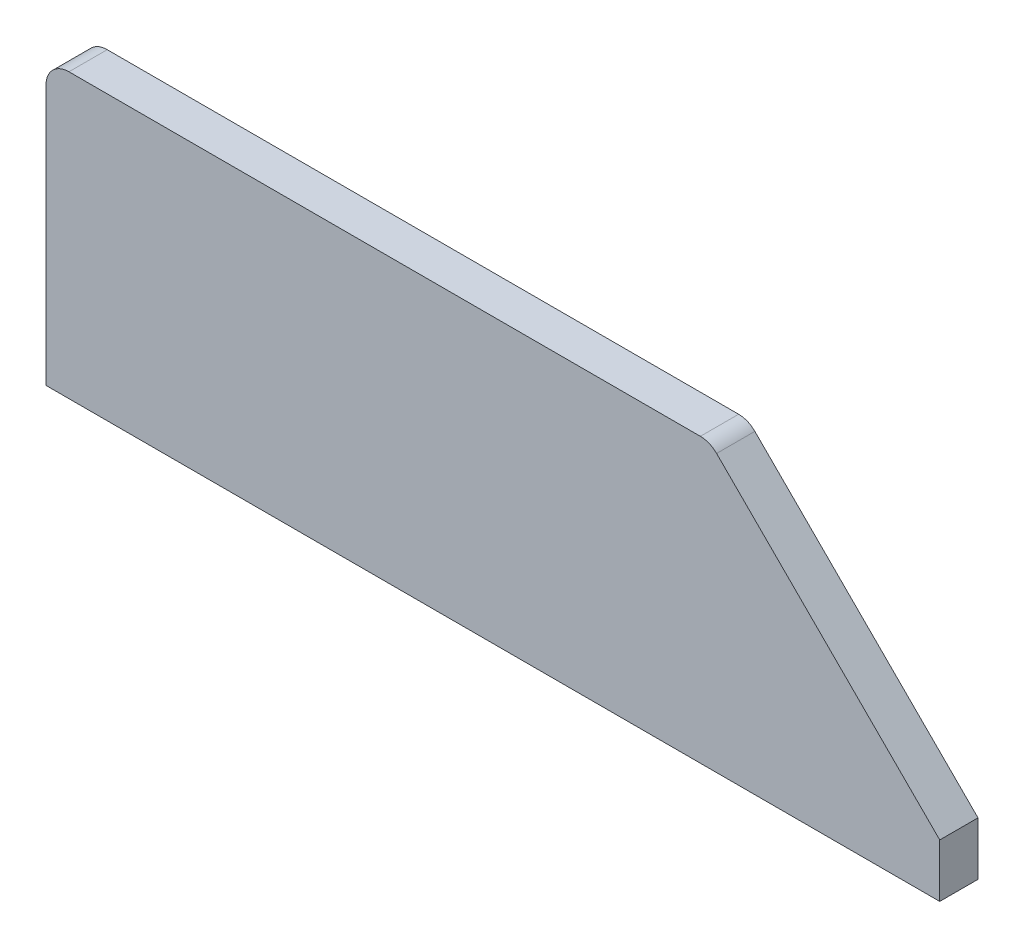
SolidWorks part; units mm, degrees
ref_plane "Alzado" through (0, 0, 0) normal (0, 0, 1) x (1, 0, 0)
ref_plane "Planta" through (0, 0, 0) normal (0, 1, 0) x (1, 0, 0)
ref_plane "Vista lateral" through (0, 0, 0) normal (1, 0, 0) x (0, 0, -1)
sketch "Croquis1" plane through (0, 0, 0) normal (0, 0, 1) x (1, 0, 0)
  point P0 (0, 0)
  line B0 (87.636, 36.1213) -> (116.7967, 6.9607)
  line B1 (3, 37) -> (85.5147, 37)
  line B2 (0, 0) -> (0, 34)
  line B3 (0, 0) -> (116.7967, 0)
  line B4 (116.7967, 0) -> (116.7967, 6.9607)
  arc B5 (87.636, 36.1213) -> (85.5147, 37) centre (85.5147, 34) ccw
  arc B6 (3, 37) -> (0, 34) centre (3, 34) ccw
sketch_block_instance "Bloque1-1"
sketch_block "Bloque1"
extrude "Saliente-Extruir1" add sketch "Croquis1" along normal blind 5
